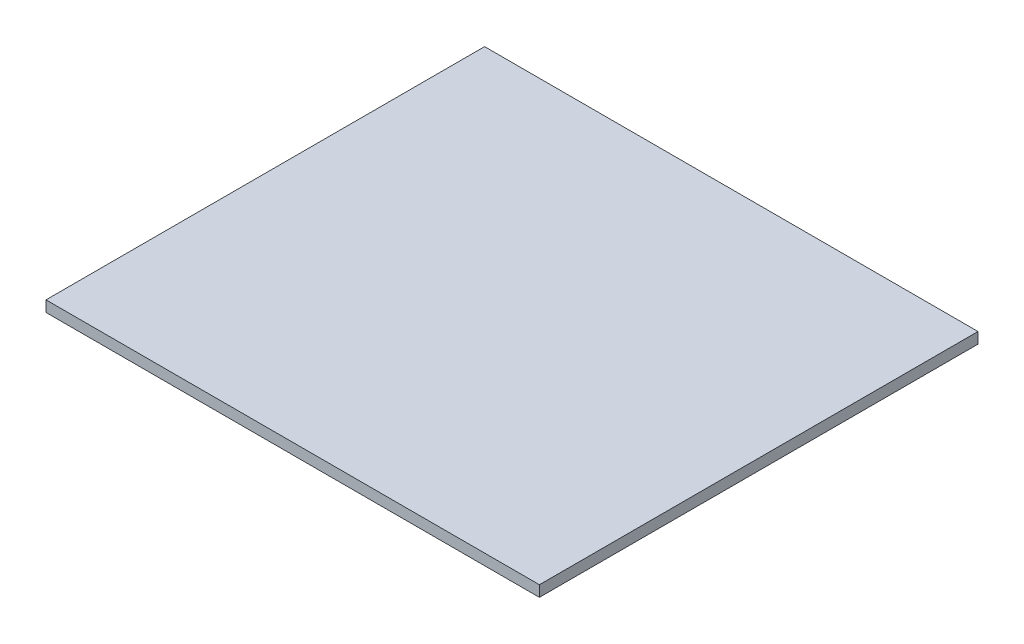
SolidWorks part; units mm, degrees
ref_plane "Front Plane" through (0, 0, 0) normal (0, 0, 1) x (1, 0, 0)
ref_plane "Top Plane" through (0, 0, 0) normal (0, 1, 0) x (1, 0, 0)
ref_plane "Right Plane" through (0, 0, 0) normal (1, 0, 0) x (0, 0, -1)
sketch "Sketch1" plane through (0, 0, 0) normal (0, 1, 0) x (1, 0, 0)
  line L1 (-60.6345, 38.1382) -> (167.9655, 38.1382)
  line L2 (-60.6345, 38.1382) -> (-60.6345, -165.0618)
  line L3 (-60.6345, -165.0618) -> (167.9655, -165.0618)
  line L4 (167.9655, 38.1382) -> (167.9655, -165.0618)
  dimension "D1" = 228.6
  dimension "D2" = 203.2
extrude "Boss-Extrude1" add sketch "Sketch1" along normal blind 5.08
